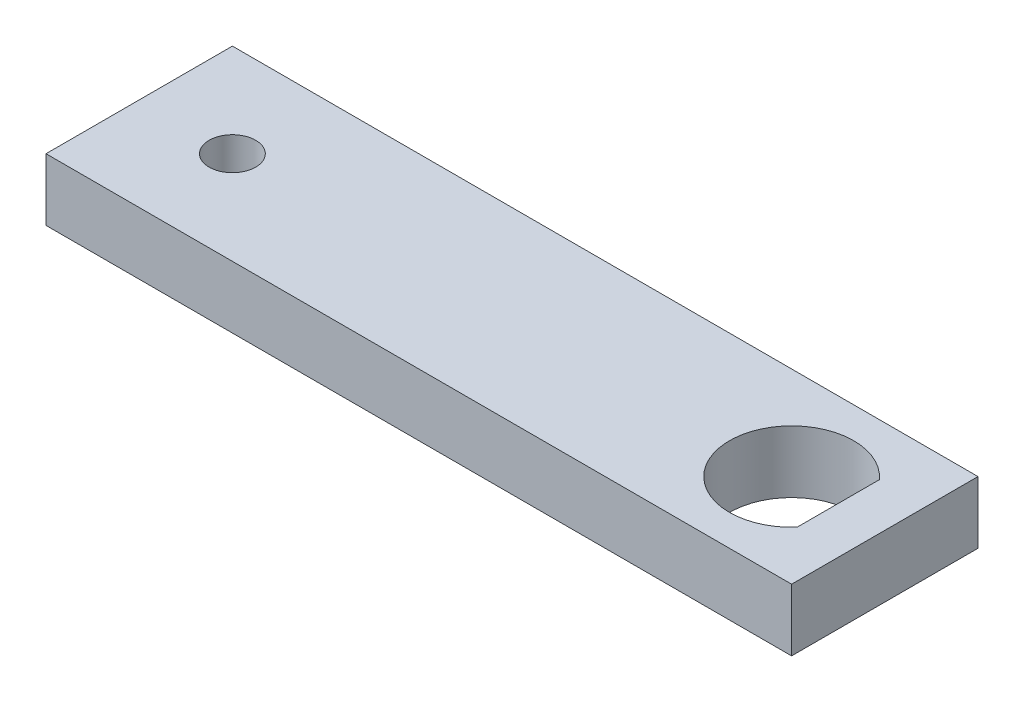
SolidWorks part; units mm, degrees
ref_plane "Front" through (0, 0, 0) normal (0, 0, 1) x (1, 0, 0)
ref_plane "Top" through (0, 0, 0) normal (0, 1, 0) x (-1, 0, 0)
ref_plane "Right" through (0, 0, 0) normal (1, 0, 0) x (0, 0, -1)
sketch "Sketch1" plane through (0, 0, 0) normal (0, 0, 1) x (1, 0, 0)
  line L0 (0, 0) -> (76.2, 0)
  line L1 (0, 0) -> (0, 6.35)
  line L2 (76.2, 6.35) -> (0, 6.35)
  line L3 (76.2, 6.35) -> (76.2, 0)
  dimension "D1" = 6.35
  dimension "D2" = 76.2
extrude "Base-Extrude" add sketch "Sketch1" along normal blind 19.05
sketch "Sketch2" plane through (0, 6.35, 0) normal (0, 1, 0) x (-1, 0, 0)
  line L0 (-76.2, 19.05) -> (-76.2, 0) construction
  line L1 (-76.2, 19.05) -> (0, 19.05) construction
  line L2 (-71.4375, 5.3249) -> (-71.4375, 13.7251)
  arc A0 (-71.4375, 5.3249) -> (-71.4375, 13.7251) centre (-66.675, 9.525) ccw
  dimension "D1" = 12.7
  dimension "D2" = 9.525
  dimension "D3" = 9.525
  dimension "D4" = 1.5875
extrude "Cut-Extrude1" cut sketch "Sketch2" against normal through all
sketch "Sketch3" plane through (0, 6.35, 0) normal (0, 1, 0) x (-1, 0, 0)
  line L0 (0, 19.05) -> (0, 0) construction
  circle A0 centre (-9.525, 9.525) radius 2.3813
  arc A1 (-71.4375, 5.3249) -> (-71.4375, 13.7251) centre (-66.675, 9.525) ccw construction
  point P5 (-66.675, 9.525)
  dimension "D1" = 4.7625
  dimension "D2" = 9.525
extrude "Cut-Extrude2" cut sketch "Sketch3" against normal through all
